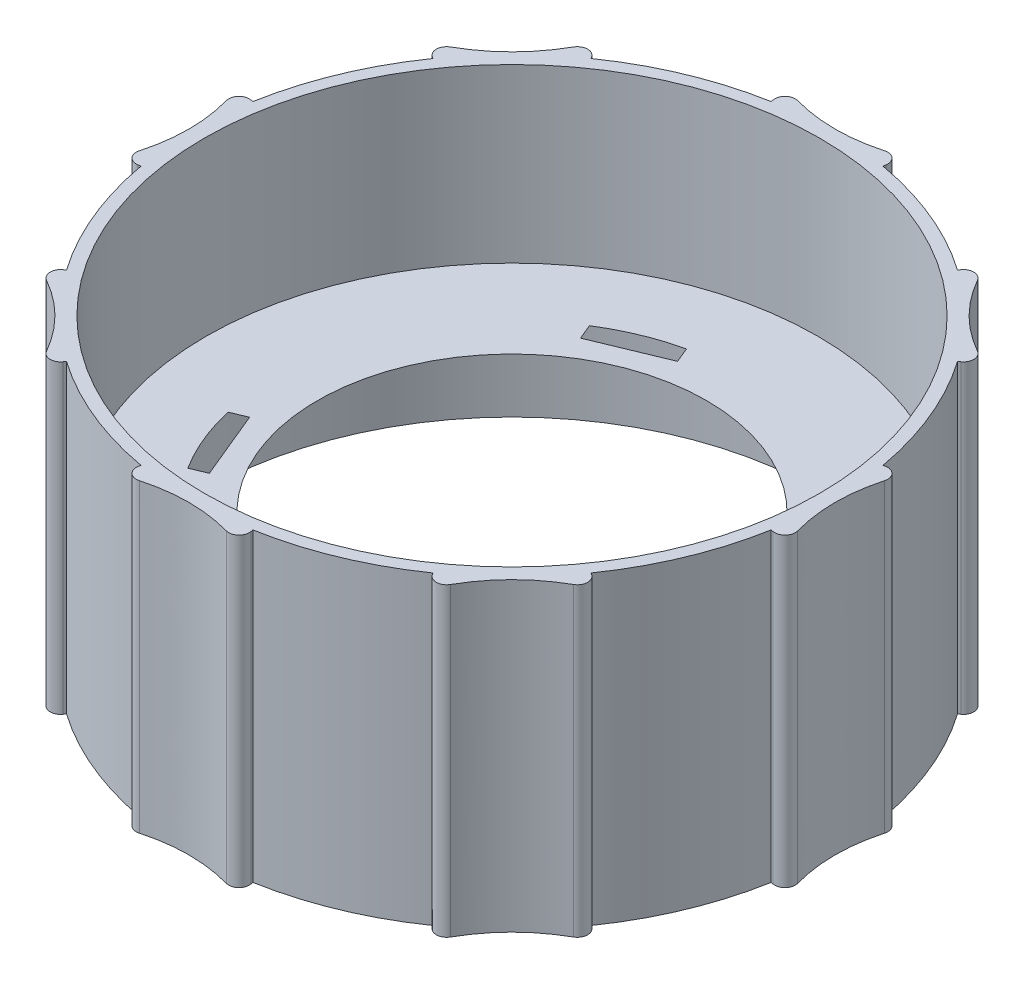
SolidWorks part; units mm, degrees
ref_plane "Front Plane" through (0, 0, 0) normal (0, 0, 1) x (1, 0, 0)
ref_plane "Top Plane" through (0, 0, 0) normal (0, 1, 0) x (1, 0, 0)
ref_plane "Right Plane" through (0, 0, 0) normal (1, 0, 0) x (0, 0, -1)
sketch "Sketch1" plane through (0, 0, 0) normal (0, 1, 0) x (1, 0, 0)
  line L0 (0, 0) -> (0, 41.6878) construction
  line L1 (0, 41.6878) -> (-77.5447, 41.6877) construction
  line L2 (8.2386, 40.7385) -> (8.4726, 41.8957)
  line L3 (0, 41.6878) -> (0, 41.8148)
  line L4 (-8.2386, 40.7385) -> (-8.6452, 41.847)
  line L5 (34.632, 22.9809) -> (35.6158, 23.6337)
  line L6 (29.4777, 29.4777) -> (29.5675, 29.5675)
  line L7 (22.9809, 34.632) -> (23.4772, 35.7033)
  line L8 (40.7385, -8.2386) -> (41.8957, -8.4726)
  line L9 (41.6878, 0) -> (41.8148, 0)
  line L10 (40.7385, 8.2386) -> (41.847, 8.6452)
  line L11 (22.9809, -34.632) -> (23.6337, -35.6158)
  line L12 (29.4777, -29.4777) -> (29.5675, -29.5675)
  line L13 (34.632, -22.9809) -> (35.7033, -23.4772)
  line L14 (-8.2386, -40.7385) -> (-8.4726, -41.8957)
  line L15 (0, -41.6878) -> (0, -41.8148)
  line L16 (8.2386, -40.7385) -> (8.6452, -41.847)
  line L17 (-34.632, -22.9809) -> (-35.6158, -23.6337)
  line L18 (-29.4777, -29.4777) -> (-29.5675, -29.5675)
  line L19 (-22.9809, -34.632) -> (-23.4772, -35.7033)
  line L20 (-40.7385, 8.2386) -> (-41.8957, 8.4726)
  line L21 (-41.6877, 0) -> (-41.8147, 0)
  line L22 (-40.7385, -8.2386) -> (-41.847, -8.6452)
  line L23 (-22.9809, 34.632) -> (-23.6337, 35.6158)
  line L24 (-29.4777, 29.4777) -> (-29.5675, 29.5675)
  line L25 (-34.632, 22.9809) -> (-35.7033, 23.4772)
  line L26 (0, 38.5636) -> (0, 41.8148) construction
  circle A0 centre (0, 0) radius 38.5636
  arc A2 (-7.1974, 43.8956) -> (-8.6452, 41.847) centre (-7.2144, 42.3717) ccw
  arc A3 (8.4726, 41.8957) -> (6.7928, 43.7104) centre (6.9789, 42.1978) ccw
  arc A4 (25.9495, 36.1283) -> (23.4772, 35.7033) centre (24.86, 35.0627) ccw
  arc A5 (35.6158, 23.6337) -> (35.7112, 26.1047) centre (34.7732, 24.9036) ccw
  arc A6 (43.8956, 7.1974) -> (41.847, 8.6452) centre (42.3717, 7.2144) ccw
  arc A7 (41.8957, -8.4726) -> (43.7104, -6.7928) centre (42.1978, -6.9789) ccw
  arc A8 (36.1283, -25.9495) -> (35.7033, -23.4772) centre (35.0627, -24.86) ccw
  arc A9 (23.6337, -35.6158) -> (26.1047, -35.7112) centre (24.9036, -34.7732) ccw
  arc A10 (7.1974, -43.8956) -> (8.6452, -41.847) centre (7.2144, -42.3717) ccw
  arc A11 (-8.4726, -41.8957) -> (-6.7928, -43.7104) centre (-6.9789, -42.1978) ccw
  arc A12 (-25.9495, -36.1283) -> (-23.4772, -35.7033) centre (-24.86, -35.0627) ccw
  arc A13 (-35.6158, -23.6337) -> (-35.7112, -26.1047) centre (-34.7732, -24.9036) ccw
  arc A14 (-43.8956, -7.1974) -> (-41.847, -8.6452) centre (-42.3717, -7.2144) ccw
  arc A15 (-41.8957, 8.4726) -> (-43.7104, 6.7928) centre (-42.1978, 6.9789) ccw
  arc A16 (-36.1283, 25.9495) -> (-35.7033, 23.4772) centre (-35.0627, 24.86) ccw
  arc A17 (-23.6337, 35.6158) -> (-26.1047, 35.7112) centre (-24.9036, 34.7732) ccw
  arc A18 (-34.632, 22.9809) -> (-40.7385, 8.2386) centre (0.0037, -0.0015) ccw
  arc A19 (-40.7385, -8.2386) -> (-34.632, -22.9809) centre (0.0037, 0.0015) ccw
  arc A20 (-22.9809, -34.632) -> (-8.2386, -40.7385) centre (0.0015, 0.0037) ccw
  arc A21 (8.2386, -40.7385) -> (22.9809, -34.632) centre (-0.0015, 0.0037) ccw
  arc A22 (34.632, -22.9809) -> (40.7385, -8.2386) centre (-0.0037, 0.0015) ccw
  arc A23 (40.7385, 8.2386) -> (34.632, 22.9809) centre (-0.0037, -0.0015) ccw
  arc A24 (22.9809, 34.632) -> (8.2386, 40.7385) centre (-0.0015, -0.0037) ccw
  arc A25 (-22.9809, 34.632) -> (-8.2386, 40.7385) centre (0.0015, -0.0037) cw
  spline S0 degree 2 poles (-7.1974, 43.8956) (-0.2208, 39.8284) (6.7928, 43.7104) knots 0 0 0 1 1 1
  spline S1 degree 2 poles (25.9495, 36.1283) (27.8368, 28.1476) (35.7112, 26.1047) knots 0 0 0 1 1 1
  spline S2 degree 2 poles (43.8956, 7.1974) (39.5869, 0.2198) (43.7104, -6.7928) knots 0 0 0 1 1 1
  spline S3 degree 2 poles (36.1283, -25.9495) (28.1476, -27.8368) (26.1047, -35.7112) knots 0 0 0 1 1 1
  spline S4 degree 2 poles (7.1974, -43.8956) (0.2198, -39.5869) (-6.7928, -43.7104) knots 0 0 0 1 1 1
  spline S5 degree 2 poles (-25.9495, -36.1283) (-27.8368, -28.1476) (-35.7112, -26.1047) knots 0 0 0 1 1 1
  spline S6 degree 2 poles (-43.8956, -7.1974) (-39.5869, -0.2198) (-43.7104, 6.7928) knots 0 0 0 1 1 1
  spline S7 degree 2 poles (-36.1283, 25.9495) (-28.1476, 27.8368) (-26.1047, 35.7112) knots 0 0 0 1 1 1
  point P95 (0, 0)
  dimension "D1" = 77.1271
  dimension "D5" = 1.524
  dimension "D3" = 1.524
  dimension "D4" = 0.127
  dimension "D6" = 1.1807
  dimension "D7" = 1.1807
  dimension "D8" = 8.2931
  dimension "D2" = 3.2512
  dimension "D9" = 8
ref_plane "Plane1" through (0, -21.0058, 0) normal (0, 1, 0) x (1, 0, 0)
sketch "Sketch2" plane through (0, -21.0058, 0) normal (0, 1, 0) x (1, 0, 0)
  line L0 (9.1613, -22.1172) -> (10.1819, -24.5812) construction
  line L1 (5.9579, -26.3308) -> (14.4058, -22.8316)
  line L2 (5.9579, -26.3308) -> (6.7355, -28.2082)
  line L3 (14.4058, -22.8316) -> (15.1835, -24.7089)
  line L4 (-26.3308, -5.9579) -> (-22.8316, -14.4058)
  line L5 (-26.3308, -5.9579) -> (-28.2082, -6.7355)
  line L6 (-22.8316, -14.4058) -> (-24.7089, -15.1835)
  line L7 (-22.1172, -9.1613) -> (-24.5812, -10.1819) construction
  line L8 (-5.9579, 26.3308) -> (-14.4058, 22.8316)
  line L9 (-5.9579, 26.3308) -> (-6.7355, 28.2082)
  line L10 (-14.4058, 22.8316) -> (-15.1835, 24.7089)
  line L11 (-9.1613, 22.1172) -> (-10.1819, 24.5812) construction
  line L12 (26.3308, 5.9579) -> (22.8316, 14.4058)
  line L13 (26.3308, 5.9579) -> (28.2082, 6.7355)
  line L14 (22.8316, 14.4058) -> (24.7089, 15.1835)
  line L15 (22.1172, 9.1613) -> (24.5812, 10.1819) construction
  circle A0 centre (0, 0) radius 37.6365
  circle A1 centre (0, 0) radius 23.9395
  arc A2 (6.7355, -28.2082) -> (15.1835, -24.7089) centre (0.6728, -1.6244) ccw
  arc A3 (-28.2082, -6.7355) -> (-24.7089, -15.1835) centre (-1.6244, -0.6728) ccw
  arc A4 (-6.7355, 28.2082) -> (-15.1835, 24.7089) centre (-0.6728, 1.6244) ccw
  arc A5 (28.2082, 6.7355) -> (24.7089, 15.1835) centre (1.6244, 0.6728) ccw
  point P9 (10.1819, -24.5812)
  point P20 (-24.5812, -10.1819)
  point P28 (-10.1819, 24.5812)
  point P36 (24.5812, 10.1819)
  point P39 (0, 0)
  dimension "D1" = 75.2729
  dimension "D2" = 47.879
  dimension "D6" = 27.2664
  dimension "D3" = 2.667
  dimension "D4" = 9.144
  dimension "D5" = 2.032
  dimension "D8" = 22.1172
  dimension "D9" = 28.2082
  dimension "D10" = 26.6065
  dimension "D11" = 29.0012
  dimension "D7" = 4
ref_plane "Plane2" through (0, -37.5666, 0) normal (0, 1, 0) x (1, 0, 0)
sketch "Sketch3" plane through (0, -37.5666, 0) normal (0, 1, 0) x (1, 0, 0)
  line L1 (22.7107, 32.5182) -> (22.5425, 32.2774)
  line L2 (-6.9349, 39.0527) -> (-6.8836, 38.7636)
  line L3 (6.9349, 39.0527) -> (6.8836, 38.7636)
  line L4 (32.5182, 22.7107) -> (32.2774, 22.5425)
  line L6 (39.0527, 6.9349) -> (38.7636, 6.8836)
  line L7 (39.0527, -6.935) -> (38.7636, -6.8836)
  line L9 (32.5182, -22.7107) -> (32.2774, -22.5425)
  line L10 (22.7107, -32.5182) -> (22.5425, -32.2774)
  line L12 (6.935, -39.0528) -> (6.8836, -38.7636)
  line L13 (-6.9349, -39.0528) -> (-6.8836, -38.7636)
  line L15 (-22.7107, -32.5182) -> (-22.5425, -32.2774)
  line L16 (-32.5182, -22.7107) -> (-32.2774, -22.5425)
  line L18 (-39.0527, -6.935) -> (-38.7636, -6.8836)
  line L19 (-39.0527, 6.9349) -> (-38.7636, 6.8836)
  line L21 (-32.5182, 22.7107) -> (-32.2774, 22.5425)
  line L22 (-22.7107, 32.5182) -> (-22.5425, 32.2774)
  arc A0 (6.8836, 38.7636) -> (22.5425, 32.2774) centre (0, 0) cw
  circle A1 centre (0, 0) radius 37.8587
  arc A2 (6.9349, 39.0527) -> (5.3476, 40.4993) centre (5.6845, 39.2748) ccw
  arc A3 (-5.3476, 40.4993) -> (-6.9349, 39.0527) centre (-5.6845, 39.2748) ccw
  arc A4 (32.5182, 22.7107) -> (32.4187, 24.856) centre (31.791, 23.7519) ccw
  arc A5 (24.856, 32.4187) -> (22.7107, 32.5182) centre (23.7519, 31.791) ccw
  arc A6 (39.0527, -6.935) -> (40.4993, -5.3476) centre (39.2748, -5.6845) ccw
  arc A7 (40.4993, 5.3476) -> (39.0527, 6.9349) centre (39.2748, 5.6845) ccw
  arc A8 (22.7107, -32.5182) -> (24.856, -32.4187) centre (23.7519, -31.791) ccw
  arc A9 (32.4187, -24.856) -> (32.5182, -22.7107) centre (31.791, -23.7519) ccw
  arc A10 (-6.9349, -39.0528) -> (-5.3476, -40.4993) centre (-5.6845, -39.2748) ccw
  arc A11 (5.3476, -40.4993) -> (6.935, -39.0528) centre (5.6845, -39.2748) ccw
  arc A12 (-32.5182, -22.7107) -> (-32.4187, -24.856) centre (-31.791, -23.7519) ccw
  arc A13 (-24.856, -32.4187) -> (-22.7107, -32.5182) centre (-23.7519, -31.791) ccw
  arc A14 (-39.0527, 6.9349) -> (-40.4993, 5.3476) centre (-39.2748, 5.6845) ccw
  arc A15 (-40.4993, -5.3476) -> (-39.0527, -6.935) centre (-39.2748, -5.6845) ccw
  arc A16 (-22.7107, 32.5182) -> (-24.856, 32.4187) centre (-23.7519, 31.791) ccw
  arc A17 (-32.4187, 24.856) -> (-32.5182, 22.7107) centre (-31.791, 23.7519) ccw
  arc A18 (-22.5425, 32.2774) -> (-6.8836, 38.7636) centre (0, 0) cw
  arc A19 (-22.7107, 32.5182) -> (-24.856, 32.4187) centre (-23.7519, 31.791) ccw [skipped]
  arc A20 (-32.4187, 24.856) -> (-32.5182, 22.7107) centre (-31.791, 23.7519) ccw [skipped]
  arc A21 (32.5182, 22.7107) -> (32.4187, 24.856) centre (31.791, 23.7519) ccw [skipped]
  arc A22 (24.856, 32.4187) -> (22.7107, 32.5182) centre (23.7519, 31.791) ccw [skipped]
  arc A23 (39.0527, -6.9349) -> (40.4993, -5.3476) centre (39.2748, -5.6845) ccw [skipped]
  arc A24 (40.4993, 5.3476) -> (39.0527, 6.9349) centre (39.2748, 5.6845) ccw [skipped]
  arc A25 (22.7107, -32.5182) -> (24.856, -32.4187) centre (23.7519, -31.791) ccw [skipped]
  arc A26 (32.4187, -24.856) -> (32.5182, -22.7107) centre (31.791, -23.7519) ccw [skipped]
  arc A27 (-6.9349, -39.0527) -> (-5.3476, -40.4993) centre (-5.6845, -39.2748) ccw [skipped]
  arc A28 (5.3476, -40.4993) -> (6.9349, -39.0527) centre (5.6845, -39.2748) ccw [skipped]
  arc A29 (-32.5182, -22.7107) -> (-32.4187, -24.856) centre (-31.791, -23.7519) ccw [skipped]
  arc A30 (-24.856, -32.4187) -> (-22.7107, -32.5182) centre (-23.7519, -31.791) ccw [skipped]
  arc A31 (-39.0527, 6.9349) -> (-40.4993, 5.3476) centre (-39.2748, 5.6845) ccw [skipped]
  arc A32 (-40.4993, -5.3476) -> (-39.0527, -6.9349) centre (-39.2748, -5.6845) ccw [skipped]
  arc A33 (32.2774, 22.5425) -> (38.7636, 6.8836) centre (0, 0) cw
  arc A34 (38.7636, -6.8836) -> (32.2774, -22.5425) centre (0, 0) cw
  arc A35 (22.5425, -32.2774) -> (6.8836, -38.7636) centre (0, 0) cw
  arc A36 (-6.8836, -38.7636) -> (-22.5425, -32.2774) centre (0, 0) cw
  arc A37 (-32.2774, -22.5425) -> (-38.7636, -6.8836) centre (0, 0) cw
  arc A38 (-38.7636, 6.8836) -> (-32.2774, 22.5425) centre (0, 0) cw
  spline S0 degree 2 poles (5.3476, 40.4993) (0, 39.0281) (-5.3476, 40.4993) knots 0.133972 0.133972 0.133972 0.866028 0.866028 0.866028
  spline S1 degree 2 poles (32.4187, 24.856) (27.597, 27.597) (24.856, 32.4187) knots 0.133972 0.133972 0.133972 0.866028 0.866028 0.866028
  spline S2 degree 2 poles (40.4993, -5.3476) (39.0281, 0) (40.4993, 5.3476) knots 0.133972 0.133972 0.133972 0.866028 0.866028 0.866028
  spline S3 degree 2 poles (24.856, -32.4187) (27.597, -27.597) (32.4187, -24.856) knots 0.133972 0.133972 0.133972 0.866028 0.866028 0.866028
  spline S4 degree 2 poles (-5.3476, -40.4993) (0, -39.0281) (5.3476, -40.4993) knots 0.133972 0.133972 0.133972 0.866028 0.866028 0.866028
  spline S5 degree 2 poles (-32.4187, -24.856) (-27.597, -27.597) (-24.856, -32.4187) knots 0.133972 0.133972 0.133972 0.866028 0.866028 0.866028
  spline S6 degree 2 poles (-40.4993, 5.3476) (-39.0281, 0) (-40.4993, -5.3476) knots 0.133972 0.133972 0.133972 0.866028 0.866028 0.866028
  spline S7 degree 2 poles (-24.856, 32.4187) (-27.597, 27.597) (-32.4187, 24.856) knots 0.133972 0.133972 0.133972 0.866028 0.866028 0.866028
  point P6 (-23.1242, 33.1102)
  point P9 (0, 39.7637)
  point P18 (-28.1172, 28.1172)
  point P19 (33.1102, 23.1242)
  point P20 (28.1172, 28.1172)
  point P21 (-39.7637, 7.0612)
  point P22 (-39.7637, 0)
  point P23 (-33.1102, -23.1242)
  point P24 (-28.1172, -28.1172)
  point P25 (-7.0612, -39.7637)
  point P26 (0, -39.7637)
  point P27 (23.1242, -33.1102)
  point P28 (28.1172, -28.1172)
  point P29 (39.7637, -7.0612)
  point P30 (39.7637, 0)
  point P37 (28.1172, 28.1172)
  point P50 (39.7637, 0)
  point P63 (28.1172, -28.1172)
  point P76 (0, -39.7637)
  point P89 (-28.1172, -28.1172)
  point P102 (-39.7637, 0)
  point P171 (-28.1172, 28.1172)
  point P180 (0, 0)
  point P195 (0, 0)
  dimension "D1" = 8
  dimension "D4" = 1.27
  dimension "D5" = 8
  dimension "D6" = 8
surface "Surface-Plane1" sketch "Sketch2"
sketch "Sketch4" plane through (0, 0, 0) normal (0, 1, 0) x (1, 0, 0)
  circle A0 centre (0, 0) radius 38.5636
curve "Helix/Spiral1" pitch 7.112 height 20.6248 turns 2.9
extrude "Boss-Extrude1" add sketch "Sketch3" along normal blind 37.5666
equation "\"D6@Sketch1\"=\"D7@Sketch1\""
